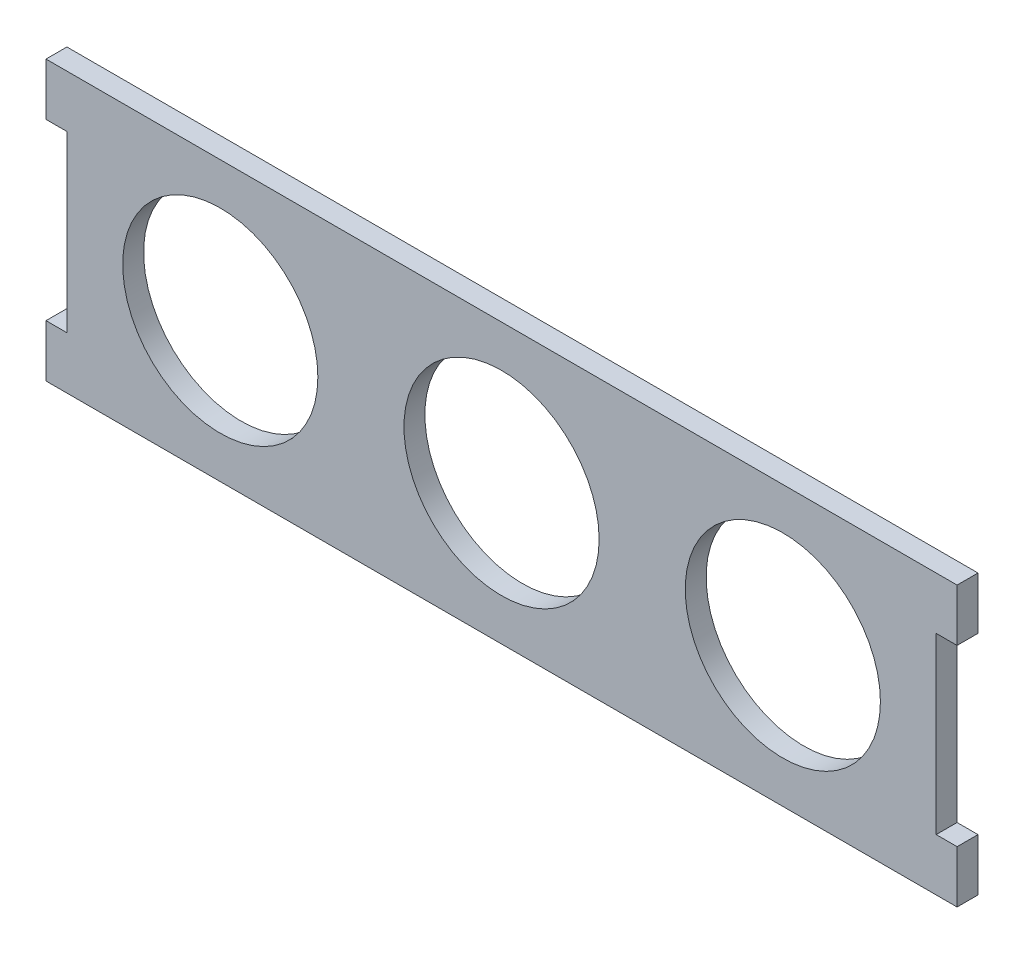
SolidWorks part; units mm, degrees
ref_plane "Front Plane" through (0, 0, 0) normal (0, 0, 1) x (1, 0, 0)
ref_plane "Top Plane" through (0, 0, 0) normal (0, 1, 0) x (1, 0, 0)
ref_plane "Right Plane" through (0, 0, 0) normal (1, 0, 0) x (0, 0, -1)
sketch "Sketch1" plane through (0, 0, 0) normal (0, 0, 1) x (1, 0, 0)
  line L0 (0, -20) -> (130.7, -20) construction
  line L1 (0, 0) -> (130.7, 0)
  line L2 (0, 0) -> (0, -40)
  line L3 (0, -40) -> (130.7, -40)
  line L4 (130.7, 0) -> (130.7, -40)
  line L5 (0, -7.5) -> (3, -7.5)
  line L6 (0, -7.5) -> (0, -32.5)
  line L7 (0, -32.5) -> (3, -32.5)
  line L8 (3, -7.5) -> (3, -32.5)
  line L9 (130.7, -7.5) -> (127.7, -7.5)
  line L10 (130.7, -7.5) -> (130.7, -32.5)
  line L11 (130.7, -32.5) -> (127.7, -32.5)
  line L12 (127.7, -7.5) -> (127.7, -32.5)
  circle A0 centre (65.35, -20) radius 14
  circle A1 centre (105.7, -20) radius 14
  circle A2 centre (25, -20) radius 14
  point P13 (3, -20)
  point P14 (130.7, -20)
  point P15 (127.7, -20)
  dimension "D5" = 28
  dimension "D6" = 28
  dimension "D7" = 28
  dimension "D1" = 130.7
  dimension "D2" = 40
  dimension "D3" = 3
  dimension "D4" = 25
  dimension "D8" = 25
  dimension "D9" = 25
extrude "Boss-Extrude1" add sketch "Sketch1" along normal blind 3 contours L8 L0 A2 A0 A1 L12 L9 L4 L1 L2 L5 | L0 L8 L7 L2 L3 L4 L11 L12 A1 A0 A2
